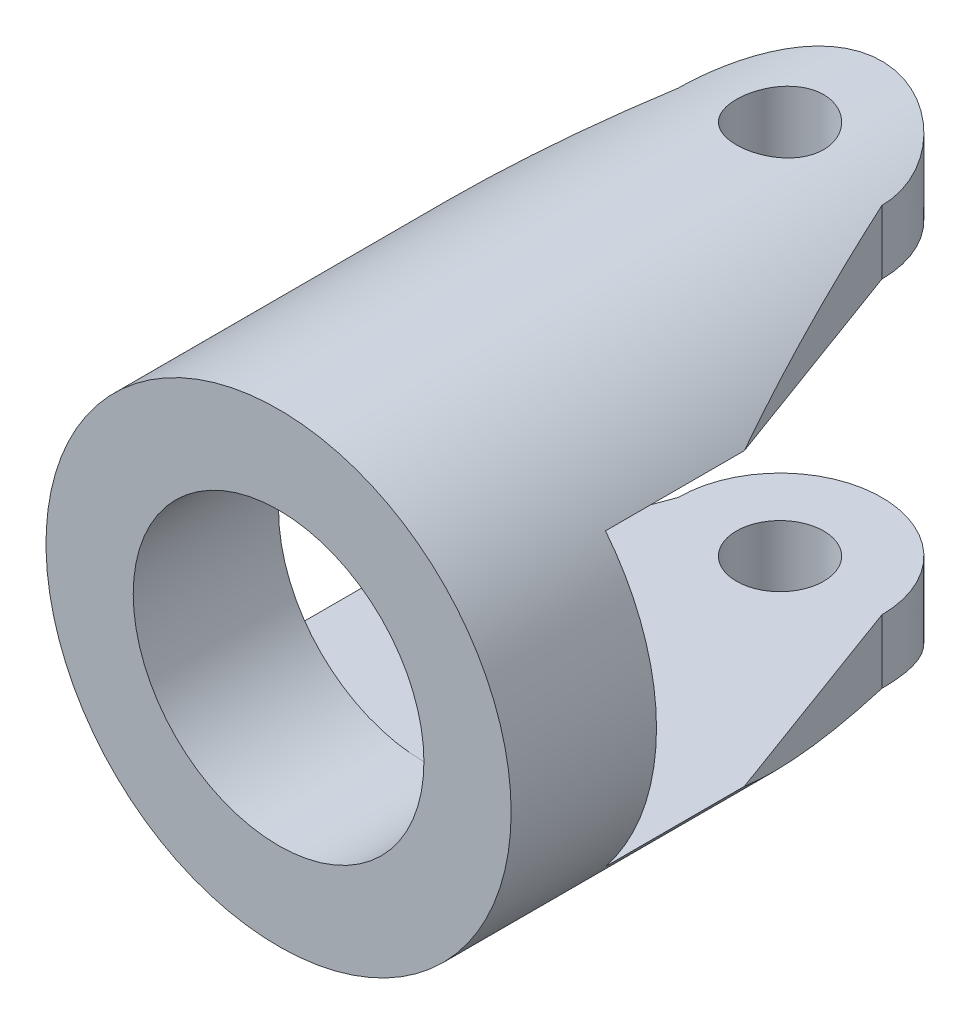
SolidWorks part; units mm, degrees
ref_plane "Front Plane" through (0, 0, 0) normal (0, 0, 1) x (1, 0, 0)
ref_plane "Top Plane" through (0, 0, 0) normal (0, 1, 0) x (1, 0, 0)
ref_plane "Right Plane" through (0, 0, 0) normal (1, 0, 0) x (0, 0, -1)
sketch "Sketch1" plane through (0, 0, 0) normal (0, 0, 1) x (1, 0, 0)
  circle A0 centre (0, 0) radius 5
  circle A1 centre (0, 0) radius 8
  dimension "D1" = 10
  dimension "D2" = 16
extrude "Boss-Extrude1" add sketch "Sketch1" along normal blind 20.75
sketch "Sketch2" plane through (0, 0, 0) normal (0, 1, 0) x (1, 0, 0)
  line L0 (0, -20.75) -> (0, -3.5) construction
  line L1 (-8, -20.75) -> (8, -20.75) construction
  line L2 (-8, -15.75) -> (8, -15.75) construction
  line L3 (-8, 0) -> (-8, -20.75) construction
  line L4 (8, -20.75) -> (8, 0) construction
  line L5 (-8, -15.75) -> (-8, 2.25)
  line L6 (-8, 2.25) -> (8, 2.25)
  line L7 (8, -15.75) -> (8, 2.25)
  line L8 (-8, -15.75) -> (-3.5, -3.5)
  line L9 (3.5, -3.5) -> (8, -15.75)
  circle A0 centre (0, -3.5) radius 1.5
  arc A1 (3.5, -3.5) -> (-3.5, -3.5) centre (0, -3.5) ccw
  arc A2 (-3.5, -3.5) -> (0, -7) centre (0, -3.5) ccw construction
  arc A3 (0, -7) -> (3.5, -3.5) centre (0, -3.5) ccw construction
  point P21 (0, 2.25)
  dimension "D1" = 3
  dimension "D3" = 2
  dimension "D2" = 17.25
  dimension "D4" = 5
  dimension "D6" = 18
extrude "Cut-Extrude1" cut sketch "Sketch2" against normal through all both and the other way through all
sketch "Sketch4" plane through (0, 0, 0) normal (1, 0, 0) x (0, 0, -1)
  line L0 (-15.75, 8) -> (-15.75, -8) construction
  line L1 (-5, 8) -> (-20.75, 8) construction
  line L2 (-20.75, -8) -> (-5, -8) construction
  line L3 (-20.75, 8) -> (-20.75, -8) construction
  line L4 (0, 5) -> (-15.75, 5)
  line L5 (-15.75, 5) -> (-15.75, -5)
  line L6 (8.8, 0) -> (-8.8, 0) construction
  line L7 (0, -5) -> (-15.75, -5)
  line L8 (0, 5) -> (0, -5)
  point P15 (-15.75, 0)
  dimension "D1" = 5
extrude "Cut-Extrude2" cut sketch "Sketch4" against normal through all both and the other way through all
